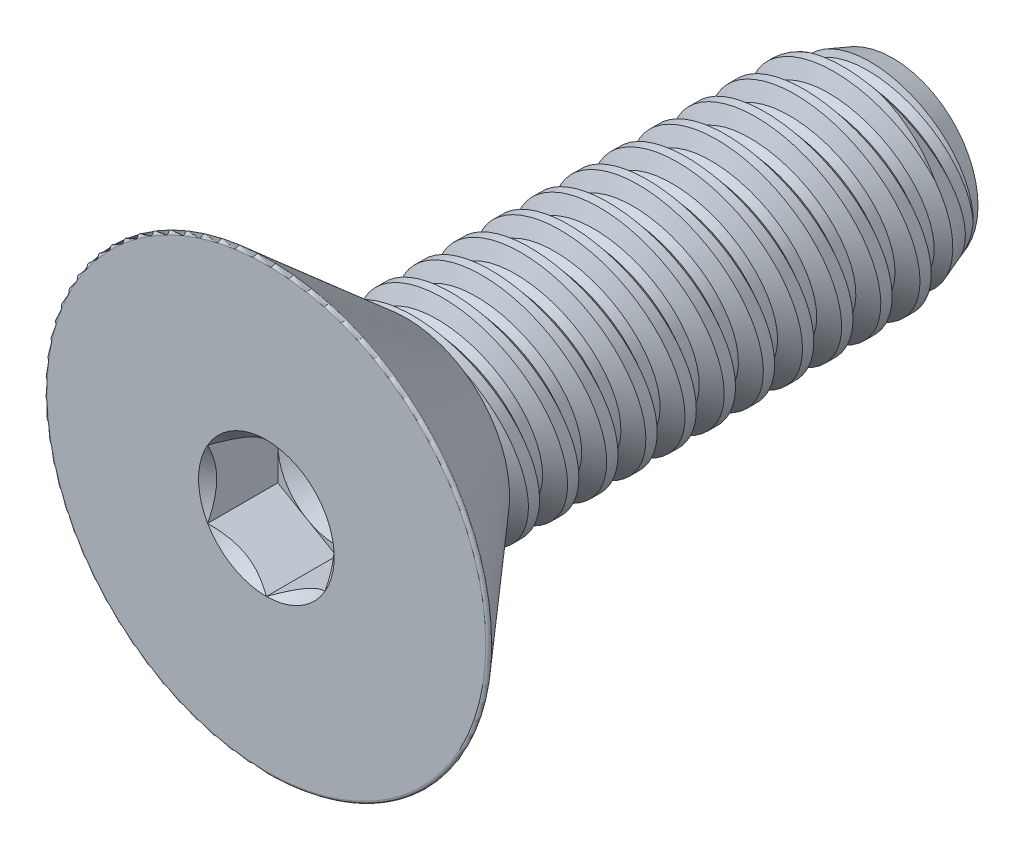
SolidWorks part; units mm, degrees
ref_plane "Front" through (0, 0, 0) normal (0, 0, 1) x (1, 0, 0)
ref_plane "Top" through (0, 0, 0) normal (0, 1, 0) x (1, 0, 0)
ref_plane "Right" through (0, 0, 0) normal (1, 0, 0) x (0, 0, -1)
sketch "Sketch1" plane through (0, 0, 0) normal (1, 0, 0) x (0, 0, -1)
  line L0 (0, 0) -> (-2.8448, 0) construction
  line L1 (0, 0) -> (9.8552, 0)
  line L2 (0, 0) -> (0, 2.0828)
  line L3 (0, 2.0828) -> (9.8552, 2.0828)
  line L4 (9.8552, 0) -> (9.8552, 2.0828)
  line L5 (0, -2.0828) -> (9.8552, -2.0828) construction
  dimension "D1" = 9.8552
  dimension "Thread Dia" = 4.1656
  dimension "Length" = 12.7
  dimension "Head Height" = 2.8448
revolve "Revolve1" add sketch "Sketch1" angle 360 about L0
ref_plane "Plane1" through (0, 0, 2.8448) normal (0, 0, 1) x (1, 0, 0)
sketch "Sketch2" plane through (0, 0, 0) normal (1, 0, 0) x (0, 0, -1)
  line L0 (0, 2.0828) -> (0, -2.0828) construction
  line L1 (0, -2.0828) -> (0.7938, -2.0828) construction
  line L2 (0.7938, -2.0828) -> (0, 2.0828) construction
  line L3 (0, 2.0828) -> (0.0975, 2.1014) construction
  line L4 (0.0975, 2.1014) -> (0.7797, 2.2314)
  line L5 (0.7797, 2.2314) -> (0.6165, 1.7629)
  line L6 (0.6165, 1.7629) -> (0.4215, 1.7258)
  line L7 (0.4215, 1.7258) -> (0.0975, 2.1014)
  line L8 (0.519, 1.7443) -> (0.4386, 2.1664) construction
  line L9 (0, -2.0828) -> (9.8552, -2.0828) construction
  line L10 (0, 2.0828) -> (9.8552, 2.0828) construction
  line L12 (0.4545, 2.0828) -> (1.2483, -2.0828) construction
  line L13 (0, -0.1622) -> (1.7028, 0.1622) construction
  line L15 (0, 0) -> (0, 2.0828) construction
  point P19 (0.8514, 0)
  dimension "D1" = 60
  dimension "Thread Pitch" = 0.7937
  dimension "D2" = 0.0992
  dimension "D3" = 0.1984
  dimension "D4" = 0.7937
revolve "Cut-Revolve1" cut sketch "Sketch2" angle 360 about L13
sketch "Sketch3" plane through (0, 0, 0) normal (1, 0, 0) x (0, 0, -1)
  line L0 (9.8552, 1.7258) -> (8.8743, 2.0828)
  line L1 (8.8743, 2.0828) -> (9.8552, 2.0828)
  line L2 (9.8552, 2.0828) -> (9.8552, 1.7258)
  line L3 (0, 2.0828) -> (9.8552, 2.0828) construction
  line L4 (9.8552, 0) -> (9.8552, 2.0828) construction
  line L5 (8.8743, 0) -> (0, 0) construction
  line L6 (8.8743, 2.0828) -> (8.8743, -2.0828) construction
  line L7 (0, -2.0828) -> (9.8552, -2.0828) construction
  dimension "D1" = 20
  dimension "D2" = 4.1656
revolve "Cut-Revolve2" cut sketch "Sketch3" angle 360 about L5
pattern_linear "LPattern1" count 12 spacing 0.7937 along (0, 0, 1)
pattern_linear "LPattern2" count 2 spacing 0.7937 along (0, 0, 1)
sketch "Sketch4" plane through (0, 0, 0) normal (0, 0, 1) x (1, 0, 0)
  circle A0 centre (0, 0) radius 4.5593
  dimension "Head Dia" = 9.1186
extrude "Extrude1" add sketch "Sketch4" along normal up to surface (2.8448 mm away)
sketch "Sketch9" plane through (0, 0, 0) normal (1, 0, 0) x (0, 0, -1)
  line L0 (-2.8448, 4.5593) -> (0, 2.0864)
  line L1 (0, 2.0864) -> (0, 4.5593)
  line L2 (0, 4.5593) -> (-2.8448, 4.5593)
  line L3 (0, 0) -> (-2.8448, 0) construction
  line L6 (-2.8448, -4.5593) -> (0, -2.0864) construction
  line L7 (0, -4.5593) -> (0, 4.5593) construction
  line L8 (-2.8448, 4.5593) -> (-2.8448, -4.5593) construction
  line L9 (0, 4.5593) -> (-2.8448, 4.5593) construction
  dimension "D1" = 82
revolve "Cut-Revolve3" cut sketch "Sketch9" angle 360 about L3
fillet "Fillet1" radius 0.0508
sketch "Sketch6" plane through (0, 0, 2.8448) normal (0, 0, 1) x (1, 0, 0)
  line L1 (0, -1.3748) -> (1.1906, -0.6874)
  line L2 (1.1906, -0.6874) -> (1.1906, 0.6874)
  line L3 (1.1906, 0.6874) -> (0, 1.3748)
  line L4 (0, 1.3748) -> (-1.1906, 0.6874)
  line L5 (-1.1906, 0.6874) -> (-1.1906, -0.6874)
  line L6 (-1.1906, -0.6874) -> (0, -1.3748)
  circle A0 centre (0, 0) radius 1.1906 construction
  dimension "Hex" = 2.3813
extrude "Cut-Extrude1" cut sketch "Sketch6" against normal blind 1.4224
sketch "Sketch7" plane through (0, 0, 2.8448) normal (0, 0, 1) x (1, 0, 0)
  circle A0 centre (0, 0) radius 1.3748
extrude "Cut-Extrude4" cut sketch "Sketch7" against normal blind 1.4224 draft 45
sketch "Sketch8" plane through (0, 0, 1.4224) normal (0, 0, 1) x (1, 0, 0)
  circle A0 centre (0, 0) radius 1.1906 construction
  circle A1 centre (0, 0) radius 1.1906
extrude "Cut-Extrude5" cut sketch "Sketch8" against normal blind 0.4741 draft 60
equation "\"D2@Sketch2\"=\"Thread Pitch@Sketch2\"/8"
equation "\"D3@Sketch2\"=\"Thread Pitch@Sketch2\"/4"
equation "\"D4@Sketch2\"=\"Thread Pitch@Sketch2\""
equation "\"D3@LPattern1\"=\"Thread Pitch@Sketch2\""
equation "\"D1@Cut-Extrude1\"=\"Head Height@Sketch1\"/2"
equation "\"D1@Cut-Extrude4\"=\"D1@Cut-Extrude1\""
equation "\"D1@Cut-Extrude5\"=\"D1@Cut-Extrude1\"/3"
equation "\"D1@LPattern1\"=\"D1@Sketch1\"/\"Thread Pitch@Sketch2\""
equation "\"D3@LPattern2\"=\"Thread Pitch@Sketch2\""
